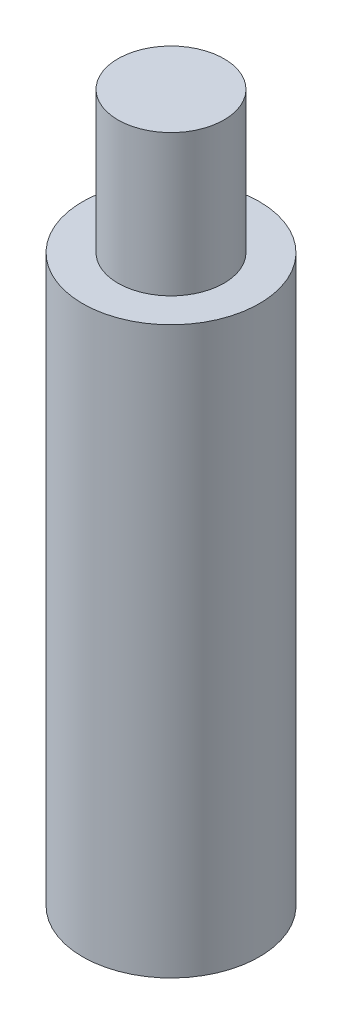
SolidWorks part; units mm, degrees
ref_plane "前视基准面" through (0, 0, 0) normal (0, 0, 1) x (1, 0, 0)
ref_plane "上视基准面" through (0, 0, 0) normal (0, 1, 0) x (1, 0, 0)
ref_plane "右视基准面" through (0, 0, 0) normal (1, 0, 0) x (0, 0, -1)
other "Configuration Table"
sketch "草图1" plane through (0, 0, 0) normal (0, 1, 0) x (1, 0, 0)
  circle A0 centre (0, 0) radius 1.5
  circle A1 centre (0, 0) radius 2.5
  dimension "D1" = 3
  dimension "D2" = 5
extrude "凸台-拉伸1" add sketch "草图1" along normal blind 16
sketch "草图2" plane through (0, 16, 0) normal (0, 1, 0) x (1, 0, 0)
  circle A0 centre (0, 0) radius 1.5
extrude "凸台-拉伸2" add sketch "草图2" along normal blind 4 separate body
